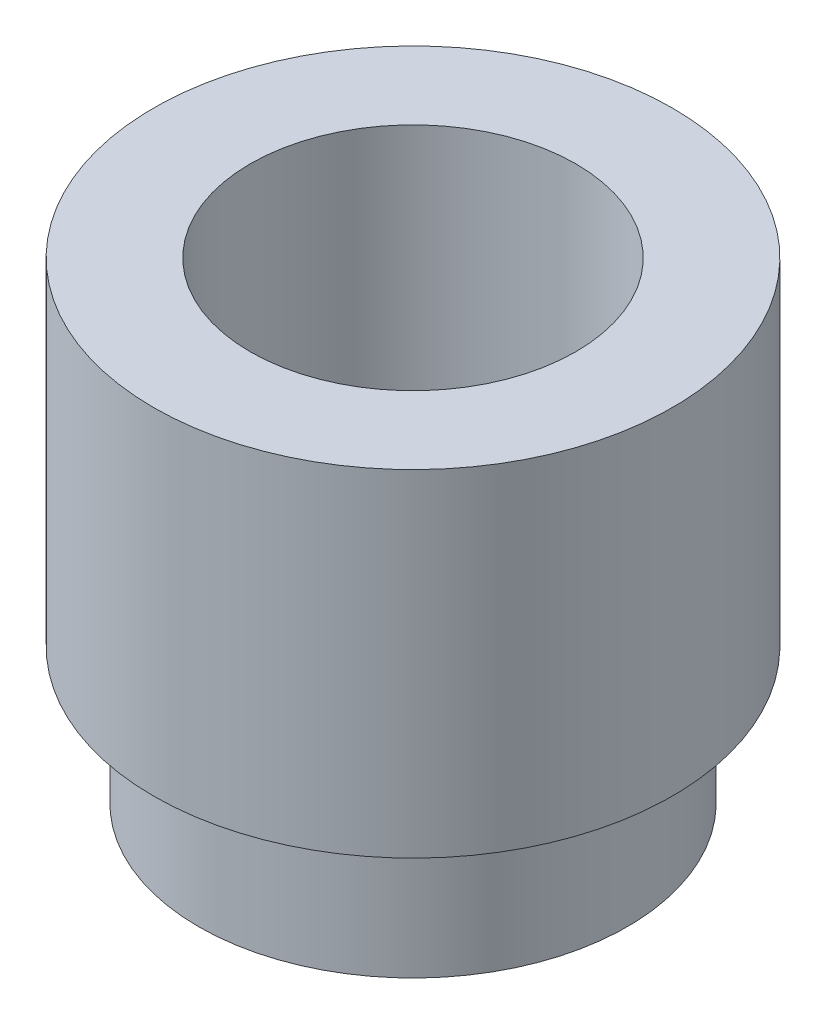
SolidWorks part; units mm, degrees
material "Brass"
ref_plane "Front Plane" through (0, 0, 0) normal (0, 0, 1) x (1, 0, 0)
ref_plane "Top Plane" through (0, 0, 0) normal (0, 1, 0) x (1, 0, 0)
ref_plane "Right Plane" through (0, 0, 0) normal (1, 0, 0) x (0, 0, -1)
sketch "Sketch1" plane through (0, 0, 0) normal (0, 0, 1) x (1, 0, 0)
  line L0 (0, 0) -> (0, 4.35) construction
  line L1 (1.5, 4.35) -> (2.39, 4.35)
  line L2 (2.39, 4.35) -> (2.39, 1.25)
  line L3 (2.39, 1.25) -> (1.975, 1.25)
  line L4 (1.975, 1.25) -> (1.975, 0)
  line L5 (1.975, 0) -> (1.5, 0)
  line L6 (1.5, 0) -> (1.5, 4.35)
  dimension "D1" = 4.78
  dimension "D2" = 4.78
  dimension "D3" = 3.1
  dimension "D4" = 4.35
  dimension "D5" = 3.95
  dimension "D6" = 3
revolve "Revolve1" add sketch "Sketch1" angle 360 about L0
